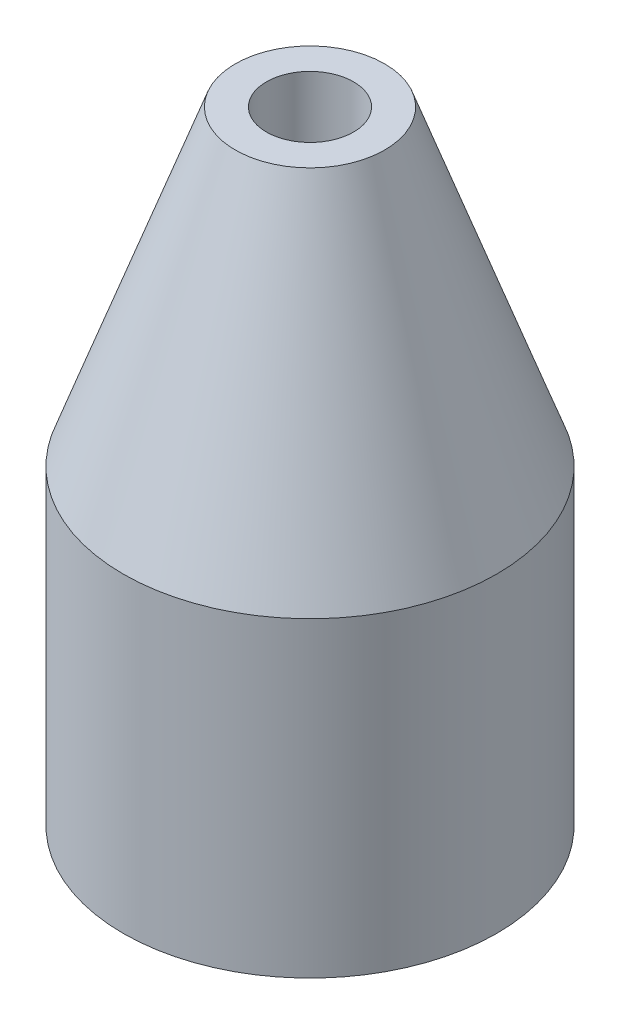
SolidWorks part; units mm, degrees
ref_plane "Front Plane" through (0, 0, 0) normal (0, 0, 1) x (1, 0, 0)
ref_plane "Top Plane" through (0, 0, 0) normal (0, 1, 0) x (1, 0, 0)
ref_plane "Right Plane" through (0, 0, 0) normal (1, 0, 0) x (0, 0, -1)
sketch "Sketch1" plane through (0, 0, 0) normal (0, 0, 1) x (1, 0, 0)
  line L0 (0, 0) -> (0, 6.35)
  line L1 (0, 0) -> (7.62, 0)
  line L2 (7.62, 0) -> (7.62, 6.35)
  line L3 (7.62, 6.35) -> (0, 6.35)
  line L4 (3.81, 0) -> (3.81, 12.7)
  line L5 (2.286, 12.7) -> (5.334, 12.7)
  line L6 (2.286, 12.7) -> (0, 6.35)
  line L7 (5.334, 12.7) -> (7.62, 6.35)
  point P10 (3.81, 12.7)
  dimension "D1" = 6.35
  dimension "D2" = 7.62
  dimension "D3" = 12.7
  dimension "D4" = 3.048
revolve "Revolve1" add sketch "Sketch1" angle 360 about L4
sketch "Sketch2" plane through (0, 12.7, 0) normal (0, 1, 0) x (1, 0, 0)
  circle A0 centre (3.81, 0) radius 0.889
  dimension "D1" = 1.778
extrude "Cut-Extrude1" cut sketch "Sketch2" against normal through all
